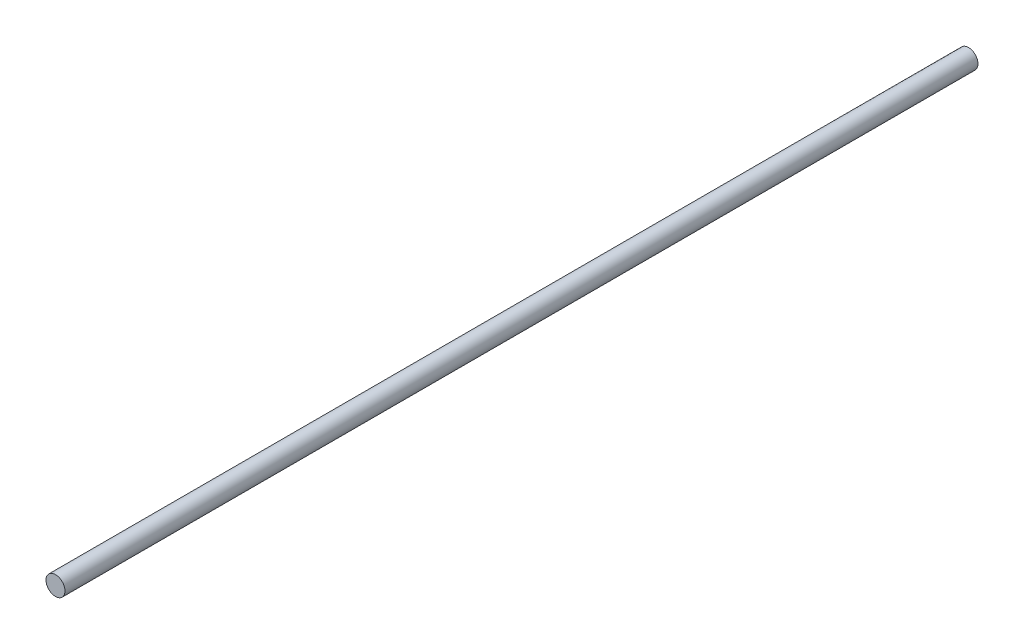
SolidWorks part; units mm, degrees
ref_plane "Plan de face" through (0, 0, 0) normal (0, 0, 1) x (1, 0, 0)
ref_plane "Plan de dessus" through (0, 0, 0) normal (0, 1, 0) x (1, 0, 0)
ref_plane "Plan de droite" through (0, 0, 0) normal (1, 0, 0) x (0, 0, -1)
sketch "Esquisse1" plane through (0, 0, 0) normal (0, 0, 1) x (1, 0, 0)
  circle A0 centre (0, 0) radius 4
  dimension "D1" = 8
sketch "Esquisse6" plane through (0, 0, 0) normal (1, 0, 0) x (0, 0, -1)
  line L0 (0, 0) -> (-384.4997, 0)
  line L2 (-384.4997, 22.0458) -> (-384.4997, -2.1542) construction
  point P6 (-384.4997, 0)
sweep "Balayage1" add profiles "Esquisse1" path "Esquisse6"
